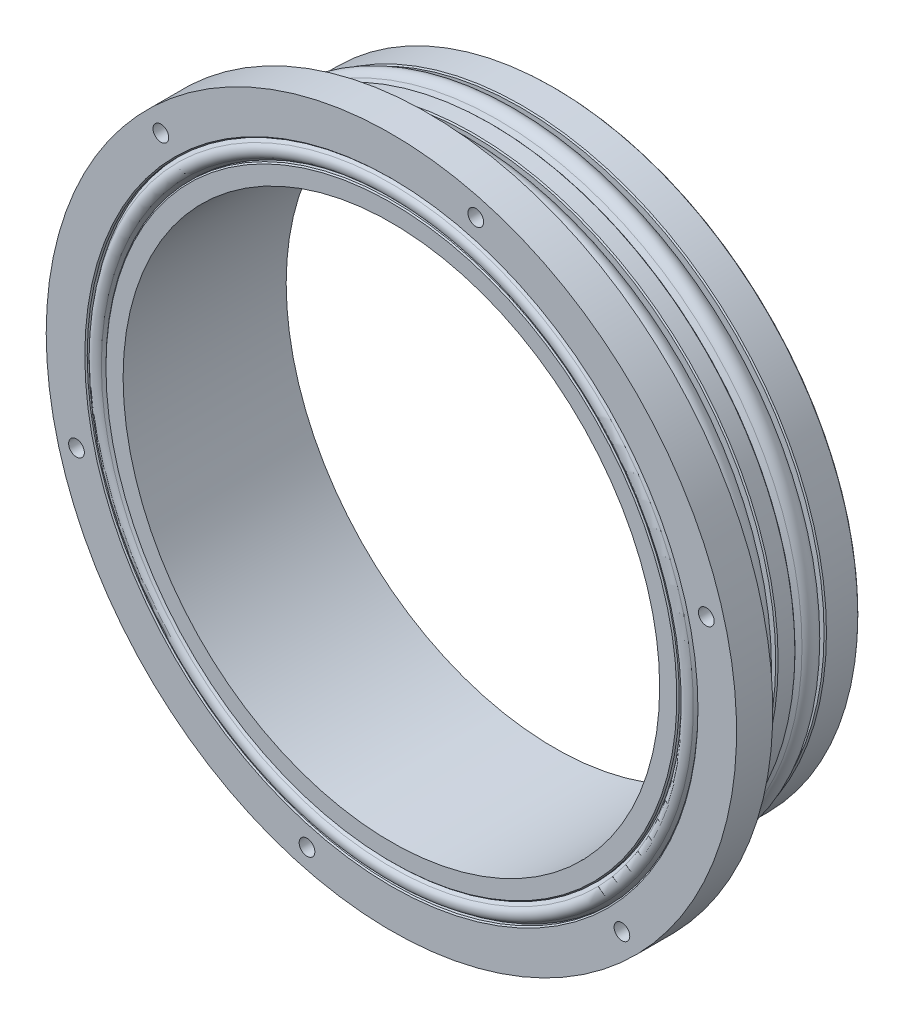
SolidWorks part; units mm, degrees
ref_plane "前视基准面" through (0, 0, 0) normal (0, 0, 1) x (1, 0, 0)
ref_plane "上视基准面" through (0, 0, 0) normal (0, 1, 0) x (1, 0, 0)
ref_plane "右视基准面" through (0, 0, 0) normal (1, 0, 0) x (0, 0, -1)
ref_plane "基准面4" through (0, 0, 0) normal (0, -1, 0) x (1, 0, 0)
sketch "草图1" plane through (0, 0, 0) normal (0, -1, 0) x (1, 0, 0)
  line L0 (47.2599, 27) -> (0, 27)
  line L1 (0, 27) -> (0, 0)
  line L2 (0, 0) -> (50.419, 0)
  line L3 (50.419, 0) -> (50.419, 5.587)
  line L4 (50.419, 5.587) -> (49.0411, 5.587)
  line L5 (49.0411, 5.587) -> (50.4317, 6.5475)
  line L6 (50.4317, 9.4525) -> (49.0411, 10.413)
  line L7 (49.0411, 10.413) -> (50.419, 10.413)
  line L8 (50.419, 10.413) -> (50.419, 13.587)
  line L9 (50.419, 13.587) -> (49.0411, 13.587)
  line L10 (49.0411, 13.587) -> (50.4317, 14.5475)
  line L11 (50.4317, 17.4525) -> (49.0411, 18.413)
  line L12 (49.0411, 18.413) -> (50.419, 18.413)
  line L13 (50.419, 18.413) -> (50.419, 21)
  line L14 (50.419, 21) -> (57.15, 21)
  line L15 (57.15, 21) -> (57.15, 27)
  line L16 (57.15, 27) -> (50.5587, 27)
  line L17 (50.5587, 27) -> (50.5587, 26.2792)
  line L18 (50.5587, 26.2792) -> (50.0138, 27.019)
  line L19 (48.0048, 27.019) -> (47.4599, 26.2792)
  line L20 (47.4599, 26.2792) -> (47.4599, 26.8)
  line L21 (47.4599, 26.8) -> (47.2599, 27)
  line L22 (0, 27.5267) -> (0, 0) construction
  arc A0 (50.4317, 6.5475) -> (50.4317, 9.4525) centre (49.4284, 8) ccw
  arc A1 (50.4317, 14.5475) -> (50.4317, 17.4525) centre (49.4284, 16) ccw
  arc A2 (50.0138, 27.019) -> (48.0048, 27.019) centre (49.0093, 26.2792) ccw
revolve "旋转1" add sketch "草图1" angle 360 about L22
hole_wizard "Ø2.6 (2.6) 直径孔1" positions "草图3" profile "草图2" hole size "Ø2.6" standard "ANSI Metric"
sketch "草图3" plane through (0, 0, 0) normal (0, 0, -1) x (-1, 0, 0)
  point P0 (-33.2269, 33.2269)
  point P1 (33.2269, 33.2269)
  point P2 (33.2269, -33.2269)
  point P3 (-33.2269, -33.2269)
sketch "草图2" plane through (33.2269, 33.2269, 0) normal (1, 0, 0) x (0, 1, 0)
  line L0 (0, 0) -> (0, 4)
  line L1 (0, 4) -> (1.3, 4)
  line L2 (1.3, 4) -> (1.3, 0)
  line L5 (1.3, 0) -> (0, 0)
  line L10 (0, 4) -> (-1.3, 4) construction
  line L11 (0, -6.35) -> (0, 107.95) construction
  dimension "孔直径" = 2.6
  dimension "孔深度" = 4
  dimension "导头角度" = 180
hole_wizard "Ø2.6 (2.6) 直径孔2" positions "草图5" profile "草图4" hole size "Ø2.6" standard "ANSI Metric"
sketch "草图5" plane through (0, 0, 21) normal (0, 0, -1) x (-1, 0, 0)
  point P0 (38.1661, 38.1661)
  point P1 (-13.9698, 52.1358)
  point P2 (-52.1358, 13.9698)
  point P3 (-38.1661, -38.1661)
  point P4 (13.9698, -52.1358)
  point P5 (52.1358, -13.9698)
sketch "草图4" plane through (-38.1661, 38.1661, 21) normal (1, 0, 0) x (0, 1, 0)
  line L0 (0, 0) -> (0, 6.5267)
  line L1 (0, 6.5267) -> (1.3, 6.5267)
  line L2 (1.3, 6.5267) -> (1.3, 0)
  line L5 (1.3, 0) -> (0, 0)
  line L11 (0, -6.35) -> (0, 107.95) construction
  dimension "通孔孔直径" = 2.6
  dimension "通孔孔深度" = 6.5267
hole_wizard "M80 间隙孔1" positions "草图7" profile "草图6" hole size "M80" standard "ANSI Metric"
sketch "草图7" plane through (0, 0, 27) normal (0, 0, 1) x (1, 0, 0)
  point P0 (0, 0)
sketch "草图6" plane through (0, 0, 27) normal (1, 0, 0) x (0, -1, 0)
  line L0 (0, 0) -> (0, 27)
  line L1 (0, 27) -> (44.419, 27)
  line L2 (44.419, 27) -> (44.419, 0)
  line L5 (44.419, 0) -> (0, 0)
  line L11 (0, -6.35) -> (0, 107.95) construction
  dimension "通孔孔直径" = 88.838
  dimension "通孔孔深度" = 27
chamfer "倒角1" distance 0.2 angle 45 6 edges at (-50.419, 0, 5.587) (-50.419, 0, 13.587) (-50.419, 0, 10.413) (-50.419, 0, 0) (-50.5587, 0, 27) (-50.419, 0, 18.413)
